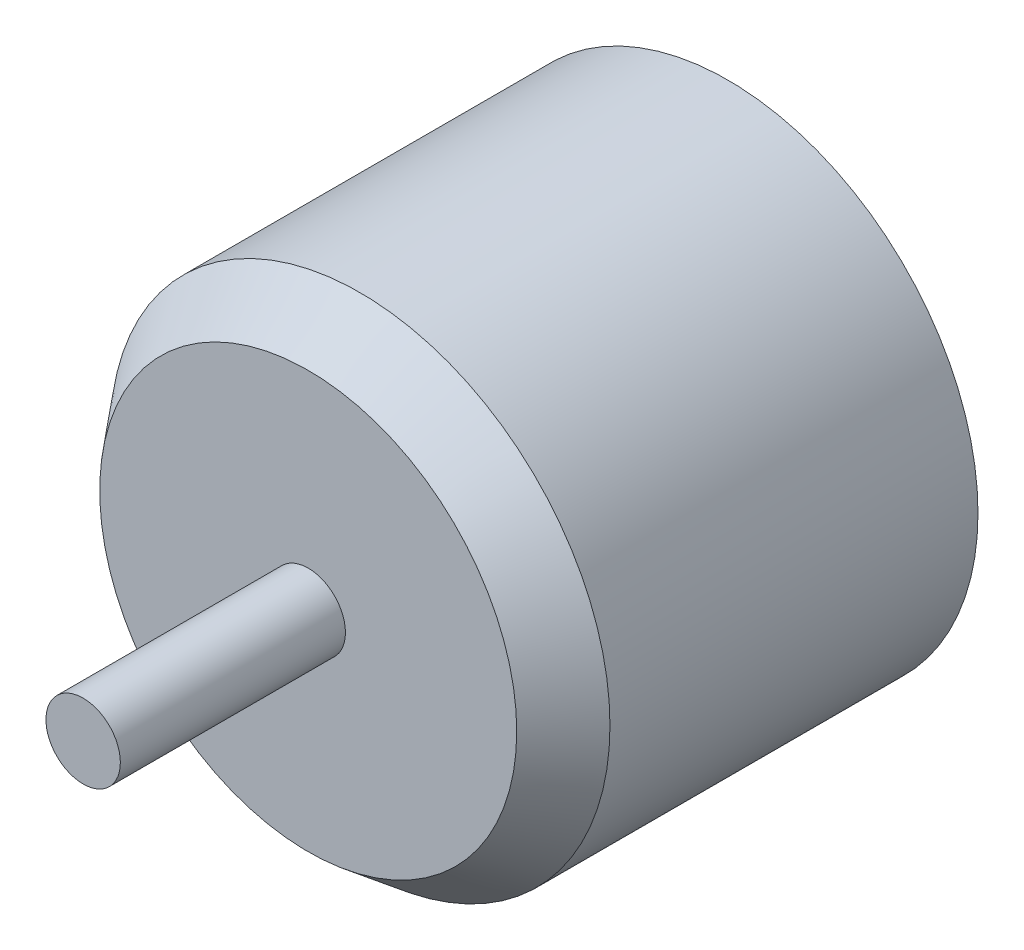
SolidWorks part; units mm, degrees
ref_plane "Front Plane" through (0, 0, 0) normal (0, 0, 1) x (1, 0, 0)
ref_plane "Top Plane" through (0, 0, 0) normal (0, 1, 0) x (1, 0, 0)
ref_plane "Right Plane" through (0, 0, 0) normal (1, 0, 0) x (0, 0, -1)
sketch "Sketch1" plane through (0, 0, 0) normal (1, 0, 0) x (0, 0, -1)
  line L0 (-67.9641, 0) -> (65.5341, 0) construction
  line L1 (-24.2, 0) -> (55, 0)
  line L2 (55, 0) -> (55, 8.9606)
  line L3 (55, 8.9606) -> (48.6, 8.9606)
  line L4 (48.6, 8.9606) -> (48.6, 18.7718)
  line L5 (48.6, 18.7718) -> (45.1235, 26.8819)
  line L6 (45.1235, 26.8819) -> (5.5586, 26.8819)
  line L7 (5.5586, 26.8819) -> (0, 22.4168)
  line L8 (0, 22.4168) -> (0, 4)
  line L9 (0, 4) -> (-24.2, 4)
  line L10 (-24.2, 4) -> (-24.2, 0)
  point P13 (0, 0)
  point P14 (-19.7741, 22.0842)
  point P15 (0, 0)
  point P16 (0, 18.5543)
  point P17 (5.5586, 26.8819)
  point P18 (0, 22.4168)
  point P19 (0, 0)
  point P20 (48.6, 18.7718)
  dimension "D1" = 48.6
  dimension "D2" = 79.2
  dimension "D3" = 26.8819
  dimension "D4" = 4
  dimension "D5" = 24.2
  dimension "D6" = 39.5649
revolve "Revolve1" add sketch "Sketch1" angle 360 about L0
